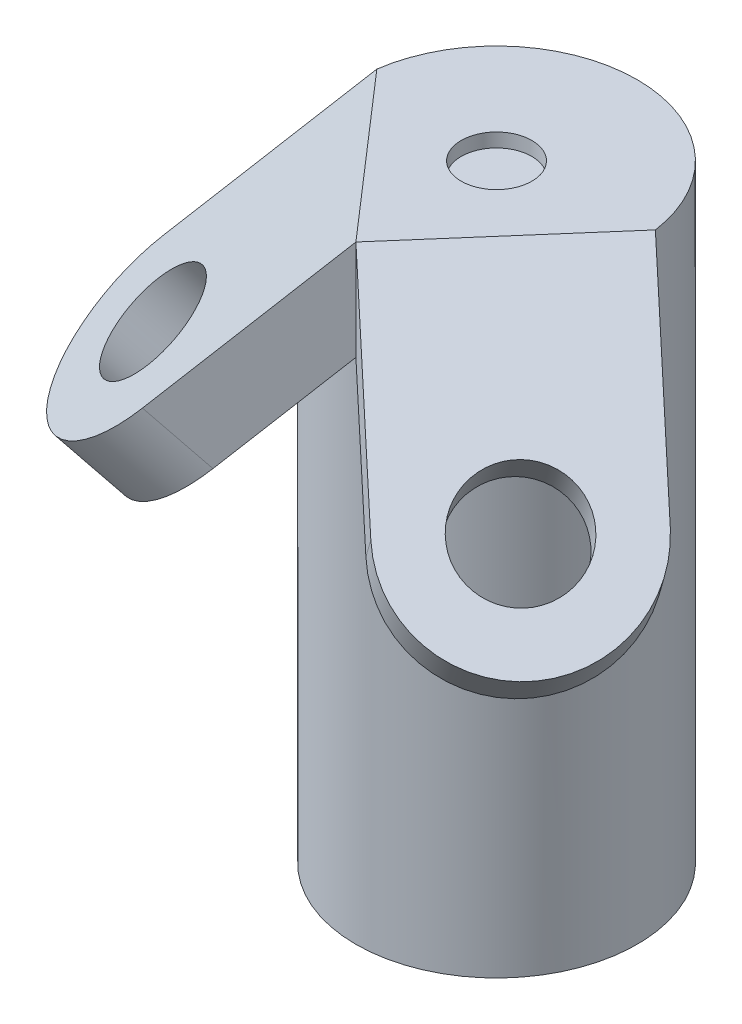
SolidWorks part; units mm, degrees
ref_plane "Piano frontale" through (0, 0, 0) normal (0, 0, 1) x (1, 0, 0)
ref_plane "Piano superiore" through (0, 0, 0) normal (0, 1, 0) x (1, 0, 0)
ref_plane "Piano destro" through (0, 0, 0) normal (1, 0, 0) x (0, 0, -1)
sketch "Schizzo1" plane through (0, 0, 0) normal (0, 0, 1) x (1, 0, 0)
  line L0 (0, 439) -> (101.5, 439)
  line L1 (0, -111.65) -> (0, 111.65) construction
  line L2 (101.5, 439) -> (101.5, 0)
  line L3 (111.65, 0) -> (-111.65, 0) construction
  line L4 (101.5, 0) -> (76, 0)
  line L5 (76, 0) -> (76, 413.5)
  line L6 (76, 413.5) -> (0, 413.5)
  line L7 (0, 413.5) -> (0, 439)
  line L8 (0, -167.2696) -> (0, 377.2162) construction
  dimension "D1" = 439
  dimension "D2" = 25.5
  dimension "D3" = 101.5
  dimension "D4" = 76
revolve "Rivoluzione1" add sketch "Schizzo1" angle 360 about L8
sketch "Schizzo2" plane through (0, 439, 0) normal (0, 1, 0) x (1, 0, 0)
  circle A0 centre (0, 0) radius 25.5
  dimension "D1" = 51
extrude "Taglio-Estrusione1" cut sketch "Schizzo2" against normal blind 10
sketch "Schizzo3" plane through (0, 439, 0) normal (0, 1, 0) x (1, 0, 0)
  line L0 (0, -101.5) -> (100.5122, 14.1261) construction
  line L3 (0, -111.65) -> (0, 111.65) construction
  circle A1 centre (0, 0) radius 101.5 construction
  point P6 (101.3836, 15.1285)
  point P7 (0, 0)
  dimension "D1" = 41
ref_plane "Piano1" through (190.7868, 252.795, 165.8484) normal (0.5337, 0.7071, 0.4639) x (0.6561, 0, -0.7547)
sketch "Schizzo4" plane through (190.7868, 252.795, 165.8484) normal (0.5337, 0.7071, 0.4639) x (0.6561, 0, -0.7547)
  line L0 (-76.603, 263.3336) -> (-76.603, 108.9279)
  line L1 (76.603, 263.3336) -> (76.603, 108.9279)
  line L2 (76.603, 263.3336) -> (-76.603, 263.3336)
  arc A0 (76.603, 108.9279) -> (-76.603, 108.9279) centre (0, 108.9279) cw
  dimension "D2" = 154.4057
extrude "Estrusione-Estrusione1" add sketch "Schizzo4" against normal blind 51
sketch "Schizzo5" plane through (190.7868, 252.795, 165.8484) normal (0.5337, 0.7071, 0.4639) x (0.8457, -0.4462, -0.2927)
  line L0 (-9.3111, 132.8406) -> (-106.7455, 252.6223) construction
  line L1 (-225.5966, 155.9449) -> (-106.7455, 252.6223) construction
  line L2 (-225.5966, 155.9449) -> (-128.1622, 36.1632) construction
  line L3 (-9.3111, 132.8406) -> (-106.7455, 252.6223)
  line L4 (-225.5966, 155.9449) -> (-106.7455, 252.6223)
  line L5 (-225.5966, 155.9449) -> (-128.1622, 36.1632)
  arc A0 (-128.1622, 36.1632) -> (-9.3111, 132.8406) centre (-68.7366, 84.5019) ccw construction
  arc A1 (-128.1622, 36.1632) -> (-9.3111, 132.8406) centre (-68.7366, 84.5019) ccw
extrude "Taglio-Estrusione2" cut sketch "Schizzo5" along normal blind 51
sketch "Schizzo6" plane through (190.7868, 252.795, 165.8484) normal (0.5337, 0.7071, 0.4639) x (0.8457, -0.4462, -0.2927)
  circle A1 centre (-68.7366, 84.5019) radius 38.5
  arc A2 (-128.1622, 36.1632) -> (-9.3111, 132.8406) centre (-68.7366, 84.5019) ccw construction
  dimension "D1" = 77
extrude "Taglio-Estrusione3" cut sketch "Schizzo6" against normal blind 51
mirror "Specchia1" about plane through (0, 0, 0) normal (1, 0, 0) of "Taglio-Estrusione3", "Taglio-Estrusione2", "Estrusione-Estrusione1"
